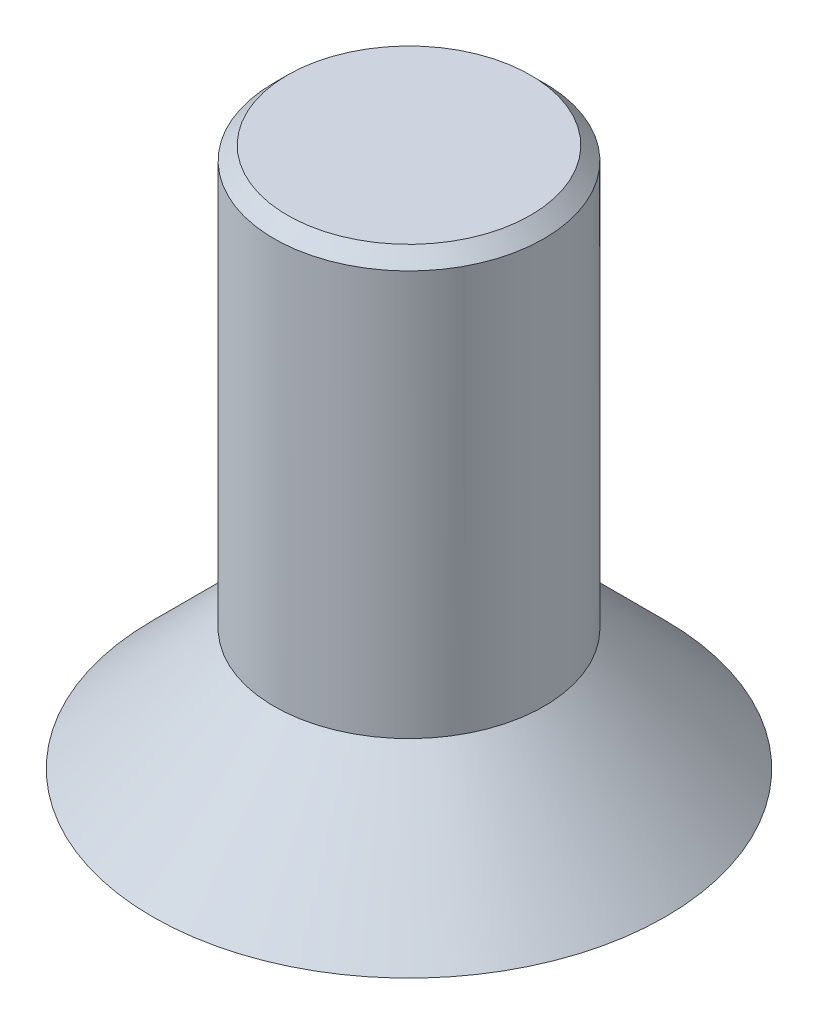
SolidWorks part; units mm, degrees
material "1.6523 (20NiCrMoS2-2)"
ref_plane "Ebene vorne" through (0, 0, 0) normal (0, 0, 1) x (1, 0, 0)
ref_plane "Ebene oben" through (0, 0, 0) normal (0, 1, 0) x (1, 0, 0)
ref_plane "Ebene rechts" through (0, 0, 0) normal (1, 0, 0) x (0, 0, -1)
sketch "Skizze1" plane through (0, 0, 0) normal (0, 0, 1) x (1, 0, 0)
  line L0 (0, 0) -> (1.9, 0)
  line L1 (1.9, 0) -> (1, 0.9)
  line L2 (1, 0.9) -> (1, 4)
  line L3 (1, 4) -> (0, 4)
  line L4 (0, 4) -> (0, 0)
  dimension "D1" = 1
  dimension "D2" = 4
  dimension "D3" = 45
  dimension "D4" = 1.9
revolve "Rotation1" add sketch "Skizze1" angle 360 about L4
sketch "Skizze2" plane through (0, 0, 0) normal (0, -1, 0) x (1, 0, 0)
  line L1 (0.7555, -0.4234) -> (0.7444, 0.4425)
  line L2 (0.7444, 0.4425) -> (-0.011, 0.866)
  line L3 (-0.011, 0.866) -> (-0.7555, 0.4234)
  line L4 (-0.7555, 0.4234) -> (-0.7444, -0.4425)
  line L5 (-0.7444, -0.4425) -> (0.011, -0.866)
  line L6 (0.011, -0.866) -> (0.7555, -0.4234)
  circle A0 centre (0, 0) radius 0.75 construction
  dimension "D1" = 1.5
extrude "Schnitt-Linear austragen1" cut sketch "Skizze2" against normal blind 1
chamfer "Fase1" distance 0.1 angle 45 1 edges at (-1, 4, 0)
